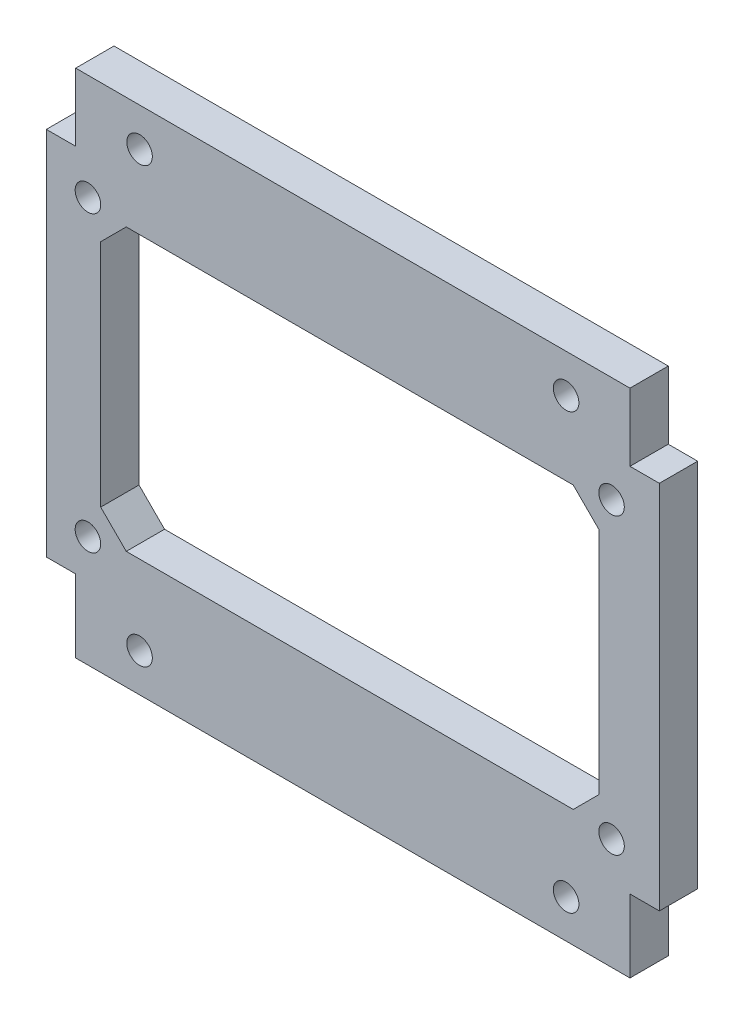
SolidWorks part; units mm, degrees
material "Acrílico (médio-alto impacto)"
ref_plane "Plano frontal" through (0, 0, 0) normal (0, 0, 1) x (1, 0, 0)
ref_plane "Plano superior" through (0, 0, 0) normal (0, 1, 0) x (1, 0, 0)
ref_plane "Plano direito" through (0, 0, 0) normal (1, 0, 0) x (0, 0, -1)
sketch "Esboço1" plane through (0, 0, 0) normal (0, 0, 1) x (1, 0, 0)
  line L0 (26.7, 0) -> (26.7, 40) construction
  line L1 (2.7, 0) -> (50.7, 0)
  line L2 (2.7, 0) -> (2.7, 40)
  line L3 (2.7, 40) -> (50.7, 40)
  line L4 (50.7, 0) -> (50.7, 40)
  dimension "D1" = 40
  dimension "D2" = 24
extrude "Ressalto-extrusão1" add sketch "Esboço1" along normal blind 3
sketch "Esboço2" plane through (0, 0, 3) normal (0, 0, 1) x (1, 0, 0)
  line L0 (26.7, 40) -> (26.7, 0) construction
  line L1 (50.7, 40) -> (2.7, 40) construction
  line L2 (2.7, 0) -> (50.7, 0) construction
  line L3 (2.7, 40) -> (2.7, 0) construction
  line L4 (2.7, 20) -> (50.7, 20) construction
  line L5 (50.7, 0) -> (50.7, 40) construction
  circle A0 centre (10, 37) radius 1
  circle A1 centre (10, 3) radius 1
  circle A2 centre (43.4, 3) radius 1
  circle A3 centre (43.4, 37) radius 1
extrude "Corte-extrusão1" cut sketch "Esboço2" against normal through all
sketch "Esboço3" plane through (0, 0, 3) normal (0, 0, 1) x (1, 0, 0)
  line L1 (48.3991, 34.698) -> (58.1933, 34.698)
  line L2 (48.3991, 34.698) -> (48.3991, 46.8976)
  line L3 (48.3991, 46.8976) -> (58.1933, 46.8976)
  line L4 (58.1933, 34.698) -> (58.1933, 46.8976)
  line L5 (48.3991, 5.698) -> (58.1933, 5.698)
  line L6 (48.3991, 5.698) -> (48.3991, -5.8426)
  line L7 (48.3991, -5.8426) -> (58.1933, -5.8426)
  line L8 (58.1933, 5.698) -> (58.1933, -5.8426)
  line L9 (4.9989, 5.698) -> (-3.9153, 5.698)
  line L10 (4.9989, 5.698) -> (4.9989, -5.8426)
  line L11 (4.9989, -5.8426) -> (-3.9153, -5.8426)
  line L12 (-3.9153, 5.698) -> (-3.9153, -5.8426)
  line L13 (4.9989, 34.698) -> (-3.9153, 34.698)
  line L14 (4.9989, 34.698) -> (4.9989, 46.8976)
  line L15 (4.9989, 46.8976) -> (-3.9153, 46.8976)
  line L16 (-3.9153, 34.698) -> (-3.9153, 46.8976)
extrude "Corte-extrusão2" cut sketch "Esboço3" against normal blind 10
sketch "Esboço4" plane through (0, 0, 3) normal (0, 0, 1) x (1, 0, 0)
  line L0 (8.9569, 31.2097) -> (6.9569, 29.2097)
  line L1 (6.9569, 29.2097) -> (6.9569, 11.2097)
  line L2 (6.9569, 11.2097) -> (8.9569, 9.2097)
  line L3 (8.9569, 9.2097) -> (43.9569, 9.2097)
  line L4 (43.9569, 9.2097) -> (45.9569, 11.2097)
  line L5 (45.9569, 11.2097) -> (45.9569, 29.2097)
  line L6 (45.9569, 29.2097) -> (43.9569, 31.2097)
  line L7 (43.9569, 31.2097) -> (8.9569, 31.2097)
extrude "Corte-extrusão3" cut sketch "Esboço4" against normal through all
sketch "Esboço5" plane through (0, 0, 3) normal (0, 0, 1) x (1, 0, 0)
  circle A0 centre (5.9569, 31.7097) radius 1
  circle A1 centre (46.9569, 31.7097) radius 0.9985
  circle A2 centre (46.9569, 8.7097) radius 1
  circle A3 centre (5.9569, 8.7097) radius 1
extrude "Corte-extrusão4" cut sketch "Esboço5" against normal through all
